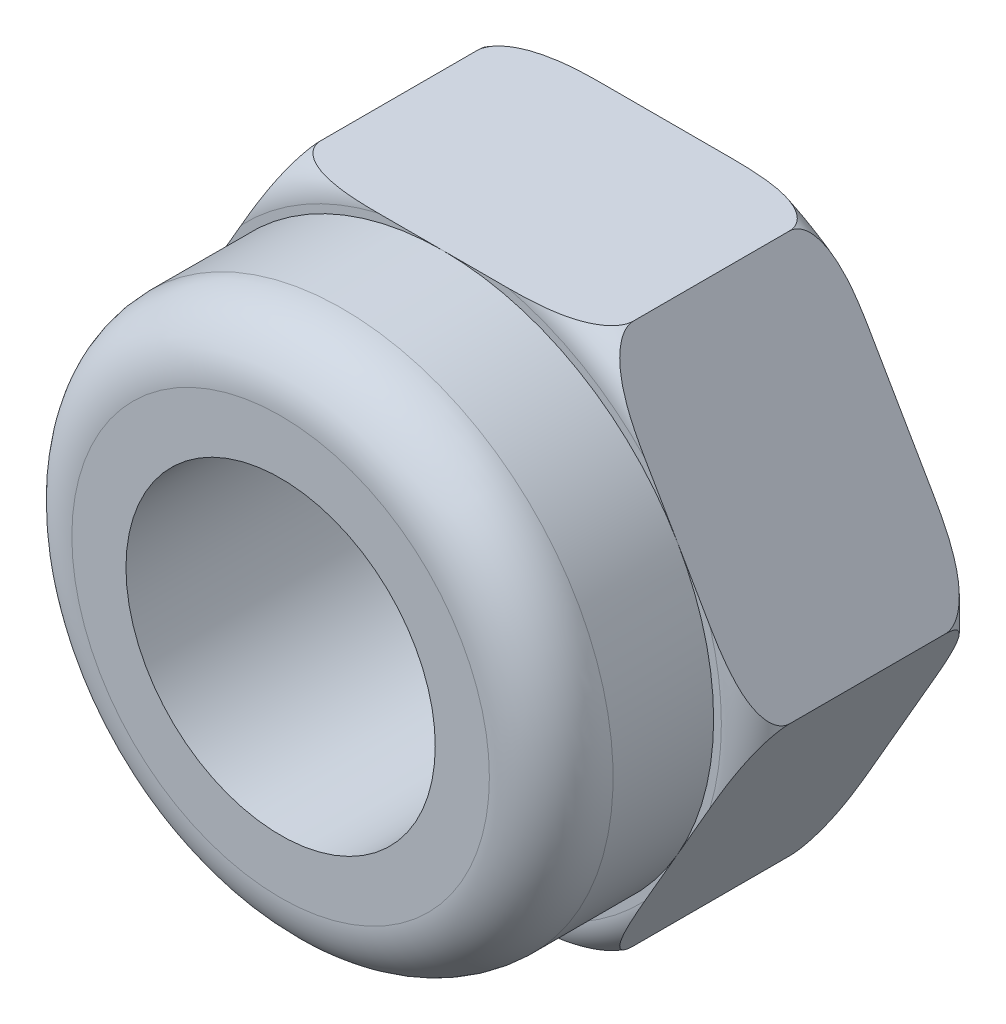
SolidWorks part; units mm, degrees
material "Stal węglowa"
ref_plane "Płaszczyzna XY" through (0, 0, 0) normal (0, 0, 1) x (1, 0, 0)
ref_plane "Płaszczyzna XZ" through (0, 0, 0) normal (0, 1, 0) x (1, 0, 0)
ref_plane "Płaszczyzna YZ" through (0, 0, 0) normal (1, 0, 0) x (0, 0, -1)
sketch "Szkic1" plane through (0, 0, 0) normal (0, 0, 1) x (1, 0, 0)
  line L1 (-4.0415, 0) -> (-2.0207, -3.5)
  line L2 (-2.0207, -3.5) -> (2.0207, -3.5)
  line L3 (2.0207, -3.5) -> (4.0415, 0)
  line L4 (4.0415, 0) -> (2.0207, 3.5)
  line L5 (2.0207, 3.5) -> (-2.0207, 3.5)
  line L6 (-2.0207, 3.5) -> (-4.0415, 0)
  circle A0 centre (0, 0) radius 3.5 construction
  circle A1 centre (0, 0) radius 2
  dimension "d" = 4
  dimension "s" = 7
extrude "Dodanie-wyciągnięcie1" add sketch "Szkic1" along normal blind 2.9
sketch "Szkic2" plane through (0, 0, 0) normal (0, 0, 1) x (1, 0, 0)
  line L0 (-2.0207, 3.5) -> (-4.0415, 0) construction
  circle A0 centre (0, 0) radius 2
  circle A1 centre (0, 0) radius 3.5
  circle A2 centre (0, 0) radius 2 construction
extrude "Dodanie-wyciągnięcie2" add sketch "Szkic2" along normal blind 5
sketch "Szkic3" plane through (0, 0, 0) normal (0, 1, 0) x (1, 0, 0)
  line L0 (-4.0415, -0.4415) -> (-4.0415, -2.4585)
  line L1 (-3.6, -2.9) -> (-2.0207, -2.9)
  line L2 (-3.6, 0) -> (-2.0207, 0)
  line L3 (0, 1.7016) -> (0, -9.3871) construction
  line L4 (-2.0207, -2.9) -> (-2.0207, 0)
  line L5 (-3.6, 0) -> (-4.0415, 0)
  line L6 (-4.0415, 0) -> (-4.0415, -2.9)
  line L7 (-4.0415, -2.9) -> (-3.6, -2.9)
  line L8 (-3.5, -2.9) -> (-3.0311, -2.9) construction
  line L9 (-3.5, -5) -> (3.5, -5) construction
  line L10 (-4.0415, -2.9) -> (-3.0311, -2.9) construction
  line L11 (-3.5, -2.9) -> (-3.5, -5) construction
  line L12 (-3.5, -2.9) -> (-3.5, -5) construction
  line L13 (-3.5, -4.2) -> (-3.5, -5)
  line L14 (-3.5, -5) -> (-2.7, -5)
  arc A0 (-4.0415, -2.4585) -> (-3.6, -2.9) centre (-3.6, -2.4585) ccw
  arc A1 (-4.0415, -0.4415) -> (-3.6, 0) centre (-3.6, -0.4415) cw
  arc A2 (-2.7, -5) -> (-3.5, -4.2) centre (-2.7, -4.2) cw
  point P13 (-4.0415, -2.9)
  point P16 (-4.0415, 0)
  dimension "D1" = 0.1
  dimension "D2" = 0.7
revolve "Wycięcie-obrót1" cut sketch "Szkic3" angle 360 about L3
equation "\"d\"=5"
